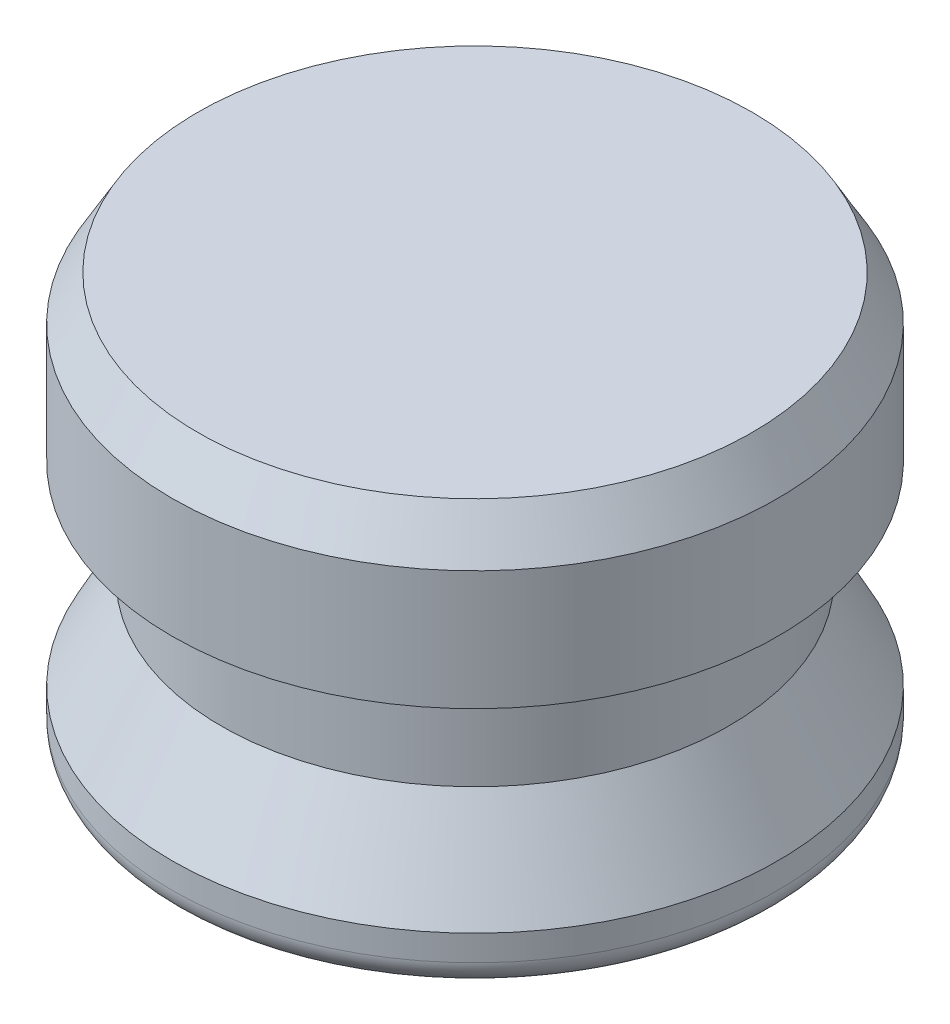
SolidWorks part; units mm, degrees
ref_plane "Front Plane" through (0, 0, 0) normal (0, 0, 1) x (1, 0, 0)
ref_plane "Top Plane" through (0, 0, 0) normal (0, 1, 0) x (1, 0, 0)
ref_plane "Right Plane" through (0, 0, 0) normal (1, 0, 0) x (0, 0, -1)
sketch "Sketch1" plane through (0, 0, 0) normal (0, 0, 1) x (1, 0, 0)
  line L0 (0, 0) -> (0, 12.7) construction
  line L1 (0, 0) -> (-9.398, 0)
  line L2 (-9.398, 0) -> (-9.398, 1.5875)
  line L4 (-7.874, 4.445) -> (-7.874, 7.62)
  line L5 (-7.874, 7.62) -> (-9.398, 7.62)
  line L6 (-9.398, 7.62) -> (-9.398, 12.7)
  line L7 (-9.398, 12.7) -> (0, 12.7)
  line L8 (-9.525, 16.6801) -> (-9.525, -9.6051) construction
  line L9 (0, 0) -> (0, 12.7)
  line L10 (-7.874, 4.445) -> (-9.398, 1.5875)
  dimension "D1" = 12.7
  dimension "D2" = 9.398
  dimension "D3" = 3.175
  dimension "D4" = 1.5875
  dimension "D5" = 9.525
  dimension "D6" = 7.874
  dimension "D7" = 7.62
revolve "Revolve1" add sketch "Sketch1" angle 360 about L9
fillet "Fillet1" radius 0.7937 1 edges at (0, 0, -9.398)
chamfer "Chamfer1" distance 0.7937 angle 60 1 edges at (0, 12.7, -9.398)
